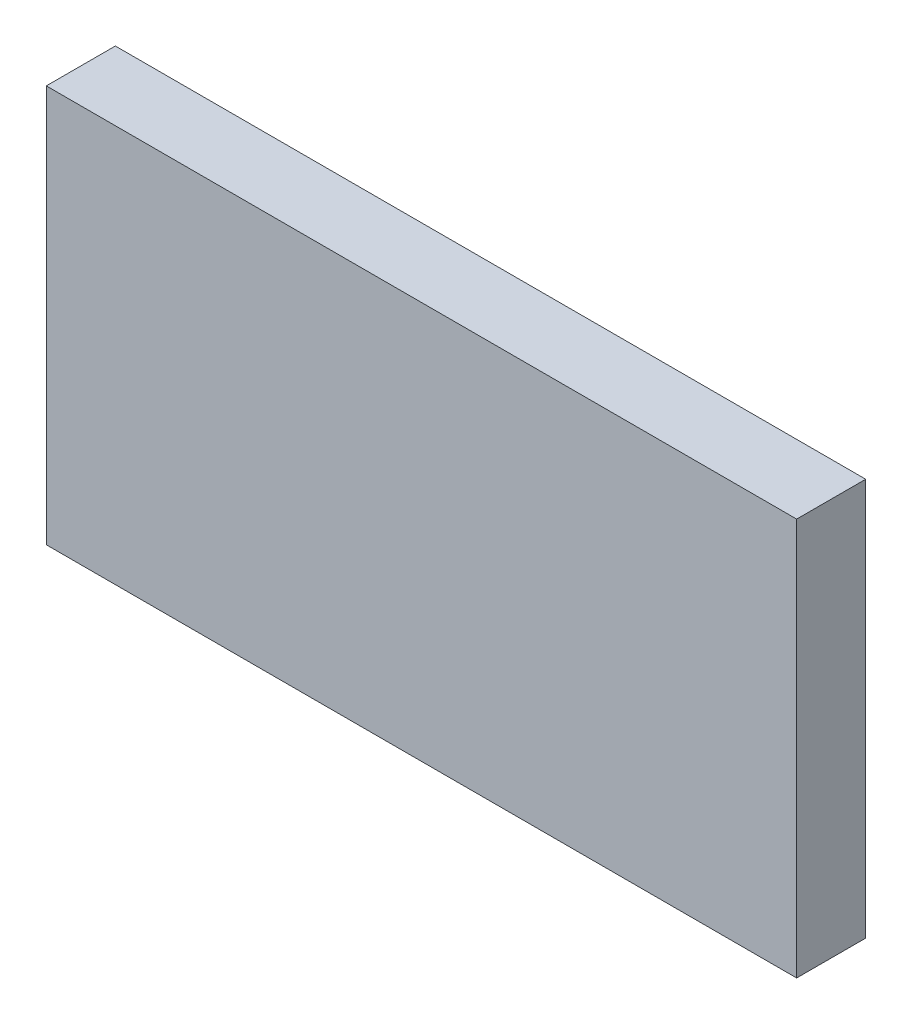
SolidWorks part; units mm, degrees
ref_plane "前基準面" through (0, 0, 0) normal (0, 0, 1) x (1, 0, 0)
ref_plane "上基準面" through (0, 0, 0) normal (0, 1, 0) x (1, 0, 0)
ref_plane "右基準面" through (0, 0, 0) normal (1, 0, 0) x (0, 0, -1)
sketch "草圖1" plane through (0, 0, 0) normal (0, 0, 1) x (1, 0, 0)
  line L1 (-54.3342, 28.7786) -> (54.3342, 28.7786)
  line L2 (-54.3342, 28.7786) -> (-54.3342, -28.7786)
  line L3 (-54.3342, -28.7786) -> (54.3342, -28.7786)
  line L4 (54.3342, 28.7786) -> (54.3342, -28.7786)
  line L5 (-54.3342, 28.7786) -> (54.3342, -28.7786) construction
  line L6 (-54.3342, -28.7786) -> (54.3342, 28.7786) construction
  point P0 (0, 0)
extrude "填料-伸長1" add sketch "草圖1" along normal blind 10
